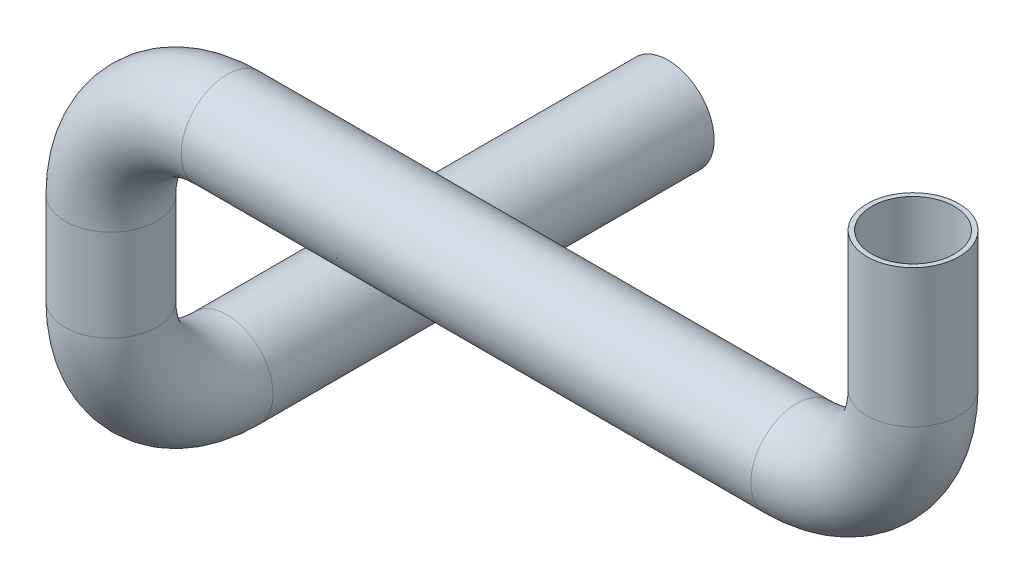
SolidWorks part; units mm, degrees
material "Beryllium Copper, UNS C17000"
ref_plane "Front Plane" through (0, 0, 0) normal (0, 0, 1) x (1, 0, 0)
ref_plane "Top Plane" through (0, 0, 0) normal (0, 1, 0) x (1, 0, 0)
ref_plane "Right Plane" through (0, 0, 0) normal (1, 0, 0) x (0, 0, -1)
sketch "Sketch1" plane through (0, 0, 0) normal (0, 0, 1) x (1, 0, 0)
  line L0 (43.65, 27.65) -> (43.65, 12.65)
  line L1 (31, 0) -> (-31, 0)
  line L2 (-43.65, -12.65) -> (-43.65, -22.65)
  arc A0 (43.65, 12.65) -> (31, 0) centre (31, 12.65) cw
  arc A1 (-31, 0) -> (-43.65, -12.65) centre (-31, -12.65) ccw
  dimension "D1" = 12.65
  dimension "D2" = 10
  dimension "D3" = 62
  dimension "D4" = 15
ref_plane "Plane1" through (0, 27.65, 0) normal (0, 1, 0) x (1, 0, 0)
sketch "Sketch2" plane through (0, 27.65, 0) normal (0, 1, 0) x (1, 0, 0)
  circle A0 centre (43.65, 0) radius 5
  dimension "D1" = 10
ref_plane "Plane2" through (-43.65, 0, 0) normal (1, 0, 0) x (0, 0, -1)
sketch "Sketch5" plane through (-43.65, 0, 0) normal (1, 0, 0) x (0, 0, -1)
  line L0 (0, -12.65) -> (0, -22.65)
  line L1 (12.65, -35.3) -> (60.65, -35.3)
  line L2 (0, -12.65) -> (0, -22.65) construction
  arc A0 (0, -22.65) -> (12.65, -35.3) centre (12.65, -22.65) ccw
  dimension "D1" = 12.65
  dimension "D2" = 10
  dimension "D3" = 48
sweep "Sweep2" add profiles "Sketch2" path "Sketch1"
sketch "Sketch6" plane through (0, -22.65, 0) normal (0, -1, 0) x (1, 0, 0)
  circle A1 centre (-43.65, 0) radius 5
  circle A2 centre (-43.65, 0) radius 5
  dimension "D1" = 0
sweep "Sweep3" add profiles "Sketch6" path "Sketch5"
shell "Shell1" thickness 0.5
